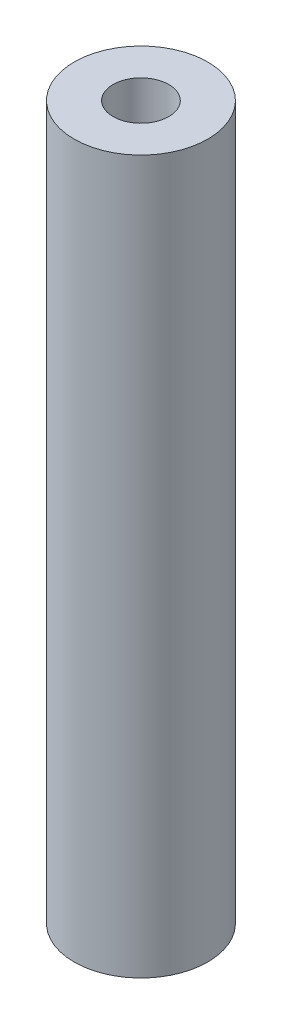
SolidWorks part; units mm, degrees
ref_plane "Front Plane" through (0, 0, 0) normal (0, 0, 1) x (1, 0, 0)
ref_plane "Top Plane" through (0, 0, 0) normal (0, 1, 0) x (1, 0, 0)
ref_plane "Right Plane" through (0, 0, 0) normal (1, 0, 0) x (0, 0, -1)
sketch "Sketch1" plane through (0, 0, 0) normal (0, 1, 0) x (1, 0, 0)
  circle A0 centre (0, 0) radius 3
  dimension "D1" = 6
extrude "Boss-Extrude1" add sketch "Sketch1" along normal blind 32
hole_wizard "Tap Drill for M3 Tap1" positions "Sketch3" profile "Sketch2" hole size "M3" standard "ISO"
sketch "Sketch3" plane through (0, 32, 0) normal (0, 1, 0) x (1, 0, 0)
  point P0 (0, 0)
sketch "Sketch2" plane through (0, 32, 0) normal (1, 0, 0) x (0, 0, 1)
  line L0 (0, 0) -> (0, 10.7511)
  line L1 (0, 10.7511) -> (1.25, 10)
  line L2 (1.25, 10) -> (1.25, 0)
  line L5 (1.25, 0) -> (0, 0)
  line L10 (0, 10.7511) -> (-1.25, 10) construction
  line L11 (0, -6.35) -> (0, 107.95) construction
  dimension "Hole Dia." = 2.5
  dimension "Hole Depth" = 10
  dimension "Drill Angle" = 118
hole_wizard "Tap Drill for M3 Tap2" positions "Sketch5" profile "Sketch4" hole size "M3" standard "ISO"
sketch "Sketch5" plane through (0, 0, 0) normal (0, -1, 0) x (-1, 0, 0)
  point P0 (0, 0)
sketch "Sketch4" plane through (0, 0, 0) normal (1, 0, 0) x (0, 0, -1)
  line L0 (0, 0) -> (0, 10.7511)
  line L1 (0, 10.7511) -> (1.25, 10)
  line L2 (1.25, 10) -> (1.25, 0)
  line L5 (1.25, 0) -> (0, 0)
  line L10 (0, 10.7511) -> (-1.25, 10) construction
  line L11 (0, -6.35) -> (0, 107.95) construction
  dimension "Hole Dia." = 2.5
  dimension "Hole Depth" = 10
  dimension "Drill Angle" = 118
